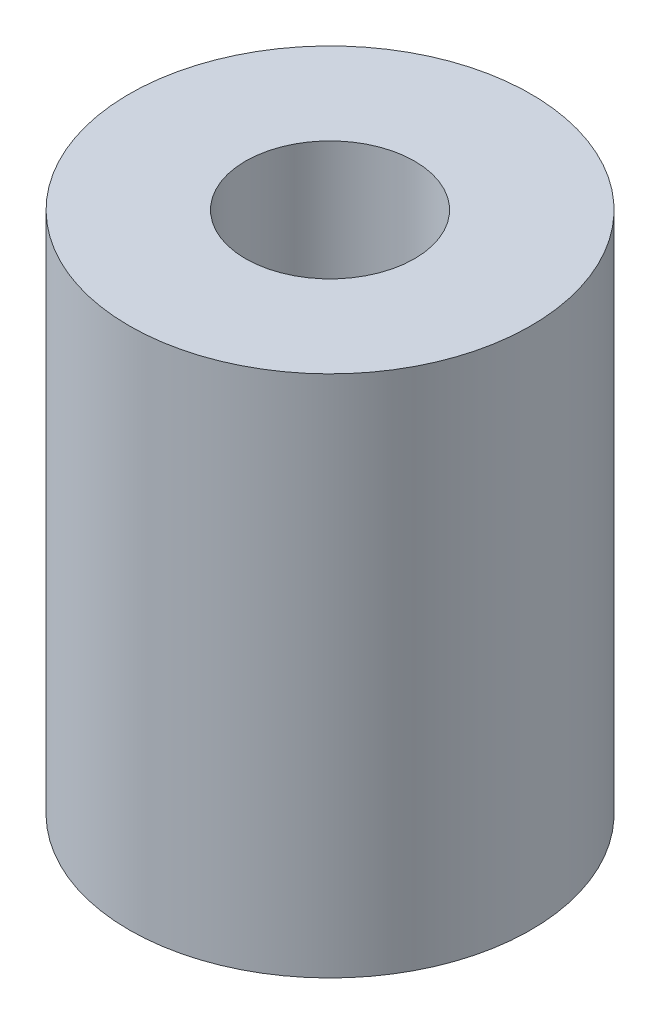
SolidWorks part; units mm, degrees
ref_plane "Front Plane" through (0, 0, 0) normal (0, 0, 1) x (1, 0, 0)
ref_plane "Top Plane" through (0, 0, 0) normal (0, 1, 0) x (1, 0, 0)
ref_plane "Right Plane" through (0, 0, 0) normal (1, 0, 0) x (0, 0, -1)
sketch "Sketch1" plane through (0, 0, 0) normal (0, 1, 0) x (1, 0, 0)
  circle A0 centre (0, 0) radius 4
  circle A1 centre (0, 0) radius 9.5
  dimension "D1" = 8
  dimension "D2" = 19
extrude "Boss-Extrude1" add sketch "Sketch1" along normal blind 24.75
